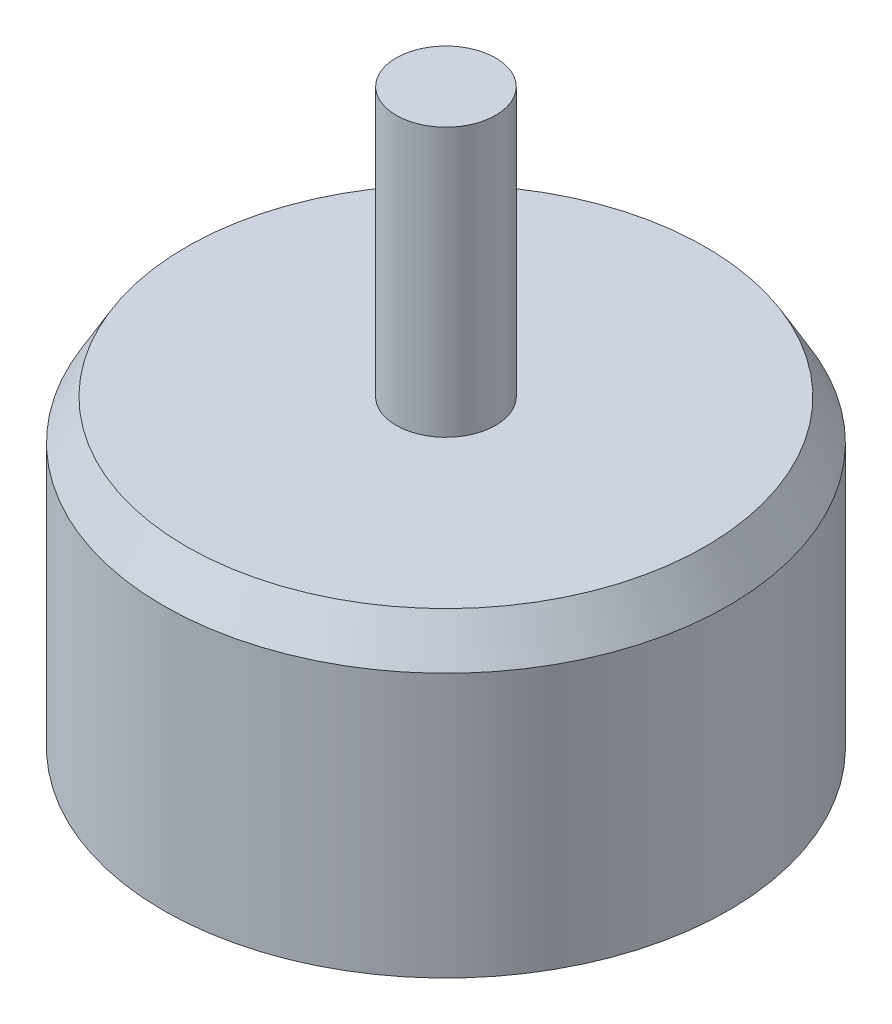
SolidWorks part; units mm, degrees
ref_plane "Front Plane" through (0, 0, 0) normal (0, 0, 1) x (1, 0, 0)
ref_plane "Top Plane" through (0, 0, 0) normal (0, 1, 0) x (1, 0, 0)
ref_plane "Right Plane" through (0, 0, 0) normal (1, 0, 0) x (0, 0, -1)
sketch "Sketch1" plane through (0, 0, 0) normal (0, 1, 0) x (1, 0, 0)
  circle A0 centre (0, 0) radius 14.2
  dimension "D1" = 28.4
extrude "Boss-Extrude1" add sketch "Sketch1" along normal blind 17
sketch "Sketch2" plane through (0, 17, 0) normal (0, 1, 0) x (1, 0, 0)
  circle A0 centre (0, 0) radius 2.5
  dimension "D1" = 5
extrude "Boss-Extrude2" add sketch "Sketch2" along normal blind 13.5
chamfer "Chamfer1" distance 2 angle 30 1 edges at (0, 17, 14.2)
sketch "Sketch3" plane through (0, 17, 0) normal (0, 1, 0) x (1, 0, 0)
  line L0 (0, 13.0453) -> (0, -13.0453) construction
  line L1 (-13.0453, 0) -> (13.0453, 0) construction
  circle A0 centre (0, 0) radius 13.0453 construction
  circle A1 centre (0, 8) radius 1.5
  circle A2 centre (9.5, 0) radius 1.5
  circle A3 centre (0, -8) radius 1.5
  circle A4 centre (-9.5, 0) radius 1.5
  circle A5 centre (0, 0) radius 2.5 construction
  dimension "D1" = 3
  dimension "D2" = 3
  dimension "D3" = 3
  dimension "D4" = 3
  dimension "D5" = 8
  dimension "D7" = 9.5
  dimension "D8" = 9.5
  dimension "D6" = 8
hole_wizard "Ø3.0 (3) Diameter Hole1" positions "Sketch5" profile "Sketch4" hole size "Ø3.0" standard "ISO"
sketch "Sketch5" plane through (0, 0, 0) normal (0, -1, 0) x (-1, 0, 0)
  point P0 (0, -8)
  point P3 (-9.5, 0)
  point P6 (0, 8)
  point P9 (9.5, 0)
sketch "Sketch4" plane through (0, 0, 8) normal (1, 0, 0) x (0, 0, -1)
  line L0 (0, 0) -> (0, 5.9013)
  line L1 (0, 5.9013) -> (1.5, 5)
  line L2 (1.5, 5) -> (1.5, 0)
  line L5 (1.5, 0) -> (0, 0)
  line L10 (0, 5.9013) -> (-1.5, 5) construction
  line L11 (0, -6.35) -> (0, 107.95) construction
  dimension "Hole Dia." = 3
  dimension "Hole Depth" = 5
  dimension "Drill Angle" = 118
chamfer "Chamfer3" distance 3 angle 30 1 edges at (0, 0, 14.2)
sketch "Sketch6" plane through (0, 0, 0) normal (0, -1, 0) x (1, 0, 0)
  circle A0 centre (0, 0) radius 5
  dimension "D1" = 10
extrude "Boss-Extrude3" add sketch "Sketch6" along normal blind 2
